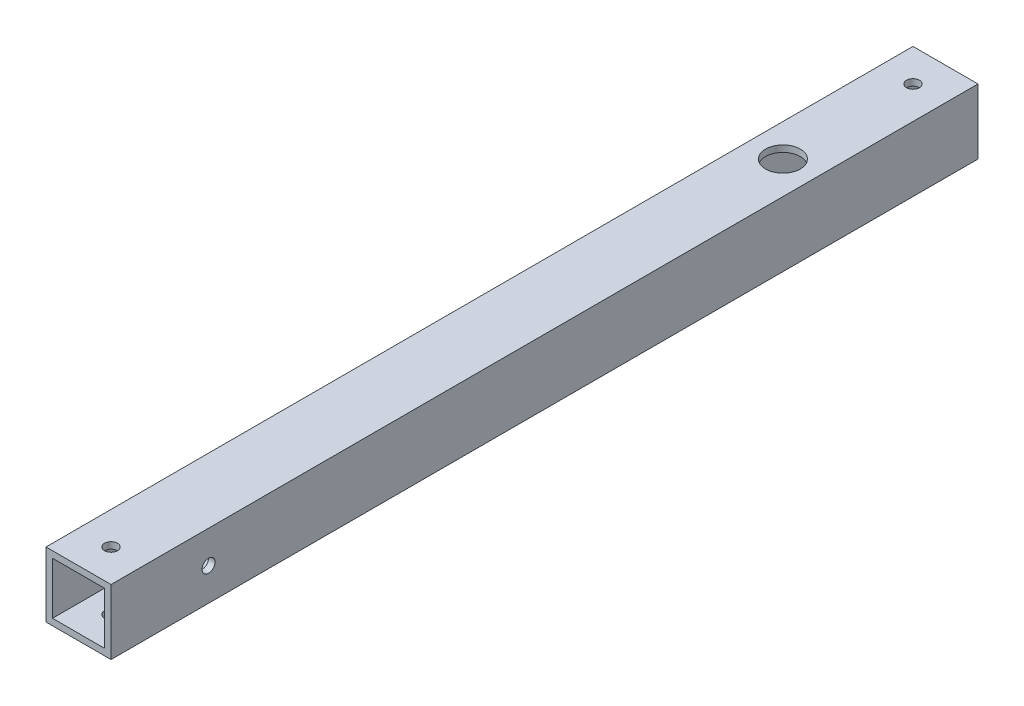
SolidWorks part; units mm, degrees
material "1060 合金"
ref_plane "正面" through (0, 0, 0) normal (0, 0, 1) x (1, 0, 0)
ref_plane "平面" through (0, 0, 0) normal (0, 1, 0) x (1, 0, 0)
ref_plane "右側面" through (0, 0, 0) normal (1, 0, 0) x (0, 0, -1)
sketch "ｽｹｯﾁ1" plane through (0, 0, 0) normal (0, 0, 1) x (1, 0, 0)
  line L1 (-7.0101, 7.7326) -> (7.9899, 7.7326)
  line L2 (-7.0101, 7.7326) -> (-7.0101, -7.2674)
  line L3 (-7.0101, -7.2674) -> (7.9899, -7.2674)
  line L4 (7.9899, 7.7326) -> (7.9899, -7.2674)
  line L9 (-5.5101, 6.2326) -> (6.4899, 6.2326)
  line L10 (-5.5101, 6.2326) -> (-5.5101, -5.7674)
  line L11 (-5.5101, -5.7674) -> (6.4899, -5.7674)
  line L12 (6.4899, 6.2326) -> (6.4899, -5.7674)
  dimension "D1" = 15
  dimension "D2" = 15
  dimension "D3" = 1.5
  dimension "D4" = 1.5
  dimension "D5" = 12
  dimension "D6" = 12
extrude "ﾎﾞｽ - 押し出し2" add sketch "ｽｹｯﾁ1" along normal blind 200
sketch "ｽｹｯﾁ2" plane through (0, 7.7326, 0) normal (0, 1, 0) x (1, 0, 0)
  line L0 (7.9899, -200) -> (-7.0101, -200) construction
  circle A0 centre (0.4899, -192.5) radius 1.5
  dimension "D1" = 7.5
extrude "ｶｯﾄ - 押し出し1" cut sketch "ｽｹｯﾁ2" against normal blind 15
sketch "ｽｹｯﾁ3" plane through (7.9899, 0, 0) normal (1, 0, 0) x (0, 0, -1)
  line L0 (-200, -7.2674) -> (-200, 7.7326) construction
  circle A0 centre (-177.5, 0.2326) radius 1.5
  dimension "D1" = 22.5
extrude "ｶｯﾄ - 押し出し2" cut sketch "ｽｹｯﾁ3" against normal blind 15
sketch "ｽｹｯﾁ4" plane through (0, 7.7326, 0) normal (0, 1, 0) x (1, 0, 0)
  line L0 (7.9899, 0) -> (-7.0101, 0) construction
  line L1 (-7.0101, -200) -> (-7.0101, 0) construction
  circle A0 centre (0.4899, -7.5) radius 1.5
  circle A1 centre (0.4899, -37.5) radius 4
  dimension "D1" = 7.5
  dimension "D2" = 30
  dimension "D3" = 7.5
extrude "ｶｯﾄ - 押し出し6" cut sketch "ｽｹｯﾁ4" against normal blind 10
sketch "ｽｹｯﾁ6" plane through (0, -7.2674, 0) normal (0, -1, 0) x (1, 0, 0)
  circle A0 centre (0.4899, 37.5) radius 1.5
  circle A1 centre (0.4899, 7.5) radius 4
  circle A2 centre (0.4899, 7.5) radius 1.5 construction
  circle A4 centre (0.4899, 37.5) radius 4 construction
  point P4 (0, 0)
  point P7 (0, 0)
  point P8 (0, 0)
extrude "ｶｯﾄ - 押し出し7" cut sketch "ｽｹｯﾁ6" against normal blind 10
